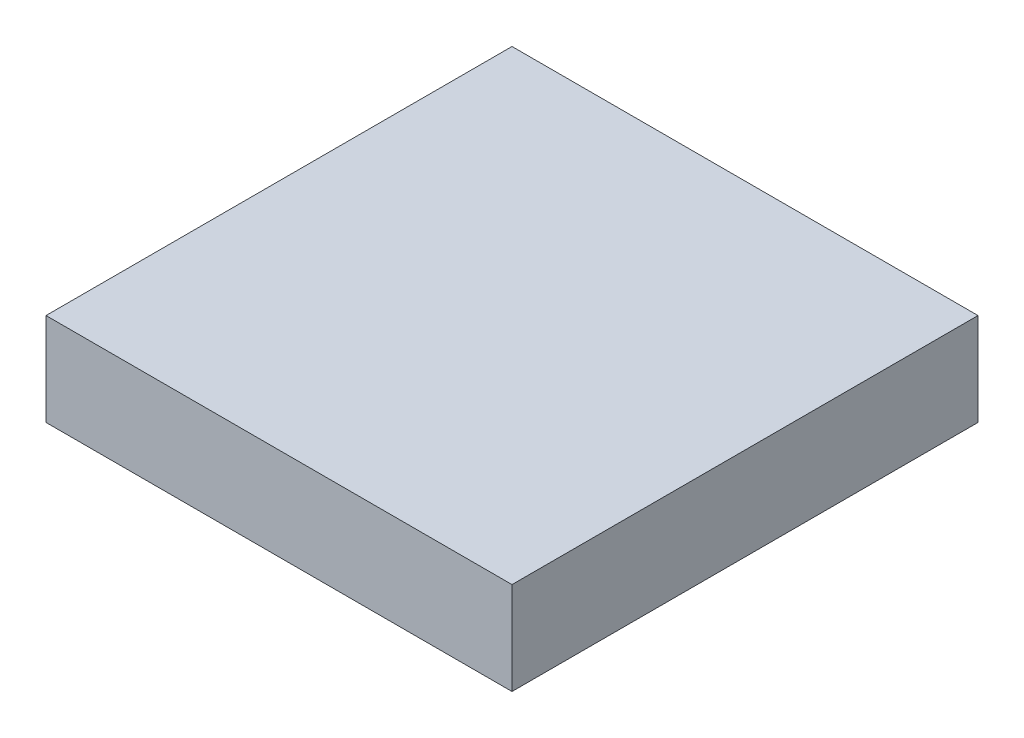
SolidWorks part; units mm, degrees
ref_plane "Front Plane" through (0, 0, 0) normal (0, 0, 1) x (1, 0, 0)
ref_plane "Top Plane" through (0, 0, 0) normal (0, 1, 0) x (1, 0, 0)
ref_plane "Right Plane" through (0, 0, 0) normal (1, 0, 0) x (0, 0, -1)
sketch "Sketch3" plane through (0, 0, 0) normal (0, 1, 0) x (1, 0, 0)
  line L1 (0, 0) -> (8, 0)
  line L2 (0, 0) -> (0, 8)
  line L3 (0, 8) -> (8, 8)
  line L4 (8, 0) -> (8, 8)
  dimension "D1" = 8
  dimension "D2" = 8
extrude "Boss-Extrude1" add sketch "Sketch3" along normal blind 1.59
sketch "Sketch7" plane through (0, 1.59, 0) normal (0, 1, 0) x (1, 0, 0)
  line L0 (1.5, 4) -> (6.5, 4)
  line L1 (0, 8) -> (0, 0) construction
  line L2 (1.5, 6.5) -> (6.5, 6.5)
  line L3 (1.5, 6.5) -> (1.5, 1.5)
  line L8 (8, 8) -> (0, 8) construction
  line L10 (1.5, 1.5) -> (6.5, 1.5)
  line L11 (6.5, 6.5) -> (6.5, 1.5)
  circle A3 centre (5.25, 2.75) radius 0.375
  circle A4 centre (5.25, 5.25) radius 0.375
  point P4 (0, 0)
  point P7 (1.5, 4)
  point P11 (4, 8)
  point P12 (4, 6.5)
  point P14 (0, 4)
  point P24 (6.5, 4)
  dimension "D5" = 1.25
  dimension "D6" = 5
  dimension "D1" = 1.25
  dimension "D3" = 0.75
  dimension "D2" = 1.25
  dimension "D4" = 5
